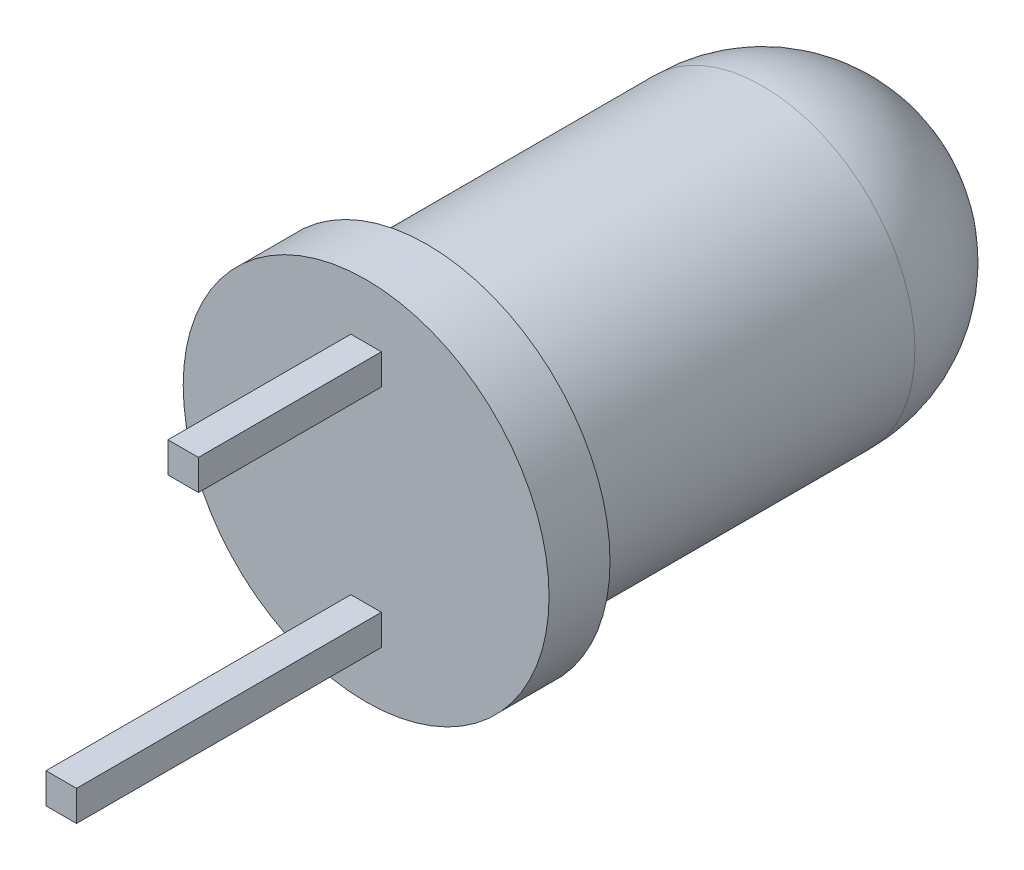
SolidWorks part; units mm, degrees
ref_plane "Спереди" through (0, 0, 0) normal (0, 0, 1) x (1, 0, 0)
ref_plane "Сверху" through (0, 0, 0) normal (0, 1, 0) x (1, 0, 0)
ref_plane "Справа" through (0, 0, 0) normal (1, 0, 0) x (0, 0, -1)
sketch "Эскиз1" plane through (0, 0, 0) normal (1, 0, 0) x (0, 0, -1)
  line L0 (0, 0) -> (0, 3)
  line L1 (0, 3) -> (1, 3)
  line L2 (1, 3) -> (1, 2.5)
  line L3 (1, 2.5) -> (9, 2.5)
  line L4 (9, 2.5) -> (9, 0)
  line L5 (9, 0) -> (0, 0)
  dimension "D1" = 2.5
  dimension "D2" = 3
  dimension "D3" = 1
  dimension "D4" = 9
revolve "Повернуть1" add sketch "Эскиз1" angle 360 about L5
fillet "Скругление1" radius 2.5 1 edges at (0, 2.5, -9)
sketch "Эскиз2" plane through (0, 0, 0) normal (0, 0, 1) x (1, 0, 0)
  line L0 (0, 1.6) -> (0, -1.6) construction
  line L1 (0, 0) -> (0.9404, 0) construction
  line L2 (-0.25, -1.6) -> (-0.25, -2.1)
  line L3 (-0.25, 1.6) -> (0.25, 1.6)
  line L4 (-0.25, 1.6) -> (-0.25, 2.1)
  line L5 (-0.25, 2.1) -> (0.25, 2.1)
  line L6 (0.25, 1.6) -> (0.25, 2.1)
  line L7 (-0.25, -1.6) -> (0.25, -1.6)
  line L8 (0.25, -1.6) -> (0.25, -2.1)
  line L9 (-0.25, -2.1) -> (0.25, -2.1)
  dimension "D1" = 3.2
  dimension "D2" = 0.5
extrude "Бобышка-Вытянуть1" add sketch "Эскиз2" along normal blind 3 separate body
sketch "Эскиз3" plane through (0, 0, 3) normal (0, 0, 1) x (1, 0, 0)
  line L4 (0.25, -1.6) -> (-0.25, -1.6)
  line L5 (-0.25, -1.6) -> (-0.25, -2.1)
  line L6 (-0.25, -2.1) -> (0.25, -2.1)
  line L7 (0.25, -2.1) -> (0.25, -1.6)
  line L8 (0.25, -1.6) -> (-0.25, -1.6)
  line L9 (-0.25, -1.6) -> (-0.25, -2.1)
  line L10 (-0.25, -2.1) -> (0.25, -2.1)
  line L11 (0.25, -2.1) -> (0.25, -1.6)
  dimension "D1" = 0
extrude "Бобышка-Вытянуть2" add sketch "Эскиз3" along normal blind 2
combine bodies "Соединить1" operation type add bodies to combine 104 105
